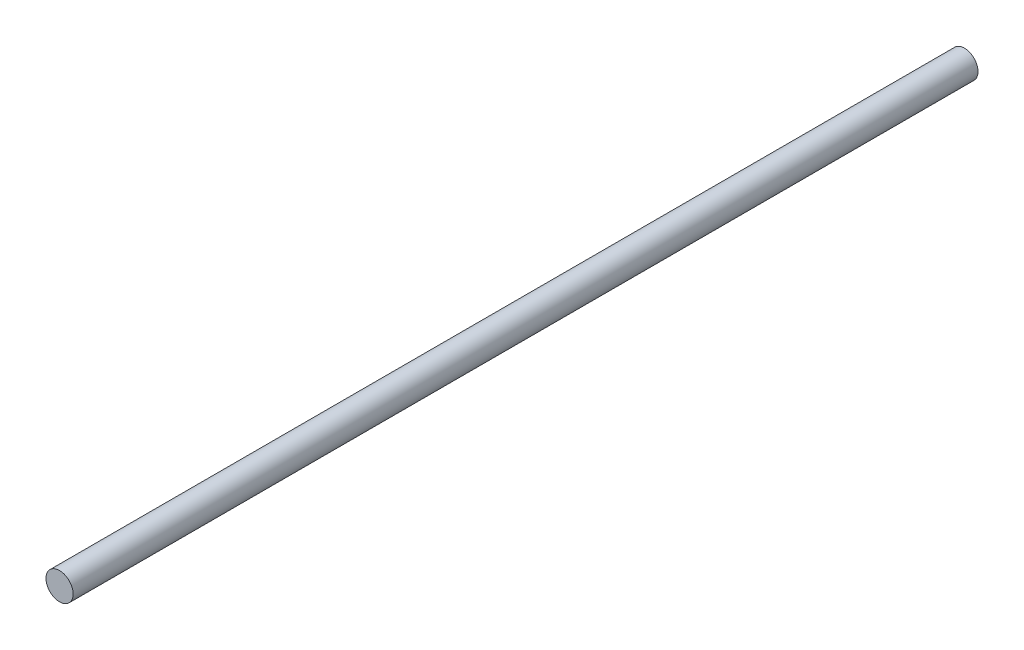
SolidWorks part; units mm, degrees
ref_plane "前视基准面" through (0, 0, 0) normal (0, 0, 1) x (1, 0, 0)
ref_plane "上视基准面" through (0, 0, 0) normal (0, 1, 0) x (1, 0, 0)
ref_plane "右视基准面" through (0, 0, 0) normal (1, 0, 0) x (0, 0, -1)
sketch "草图1" plane through (0, 0, 0) normal (0, 0, 1) x (1, 0, 0)
  circle A0 centre (0, 0) radius 3
  dimension "D1" = 6
extrude "凸台-拉伸1" add sketch "草图1" along normal blind 200
